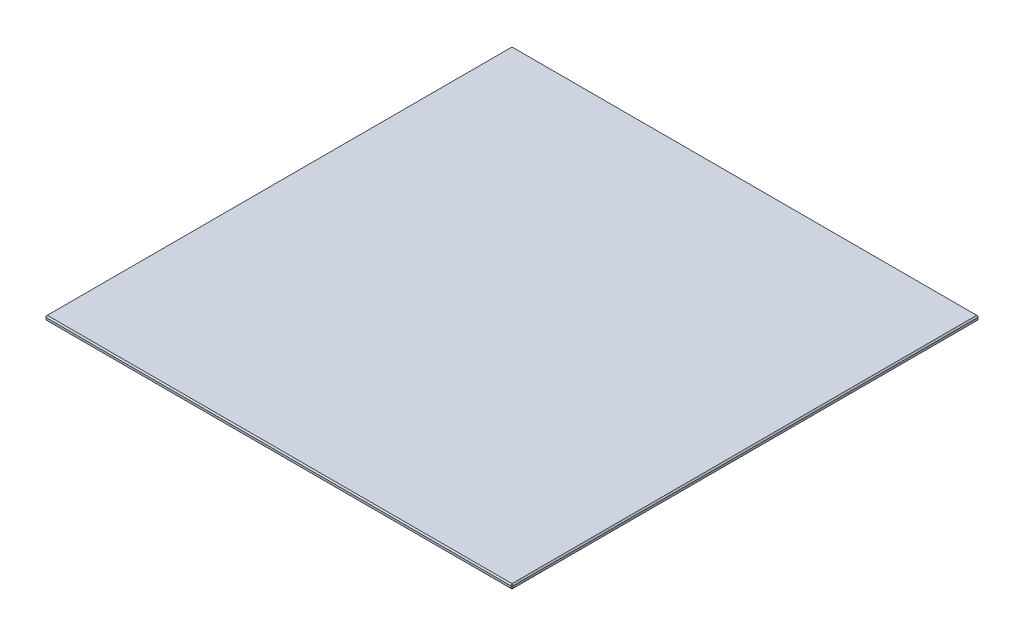
SolidWorks part; units mm, degrees
ref_plane "Front Plane" through (0, 0, 0) normal (0, 0, 1) x (1, 0, 0)
ref_plane "Top Plane" through (0, 0, 0) normal (0, 1, 0) x (1, 0, 0)
ref_plane "Right Plane" through (0, 0, 0) normal (1, 0, 0) x (0, 0, -1)
sketch "Sketch1" plane through (0, 0, 0) normal (0, 1, 0) x (1, 0, 0)
  line L1 (-150, 150) -> (150, 150)
  line L2 (-150, 150) -> (-150, -150)
  line L3 (-150, -150) -> (150, -150)
  line L4 (150, 150) -> (150, -150)
  dimension "D1" = 300
  dimension "D2" = 150
  dimension "D3" = 300
  dimension "D4" = 150
extrude "Boss-Extrude1" add sketch "Sketch1" along normal blind 3
chamfer "Chamfer1" distance 0.8 angle 45 12 edges at (150, 1.5, 150) (150, 0, 0) (150, 3, 0) (150, 1.5, -150) (0, 0, -150) (0, 3, -150) (-150, 1.5, -150) (-150, 0, 0) (0, 0, 150) (-150, 1.5, 150) (-150, 3, 0) (0, 3, 150)
